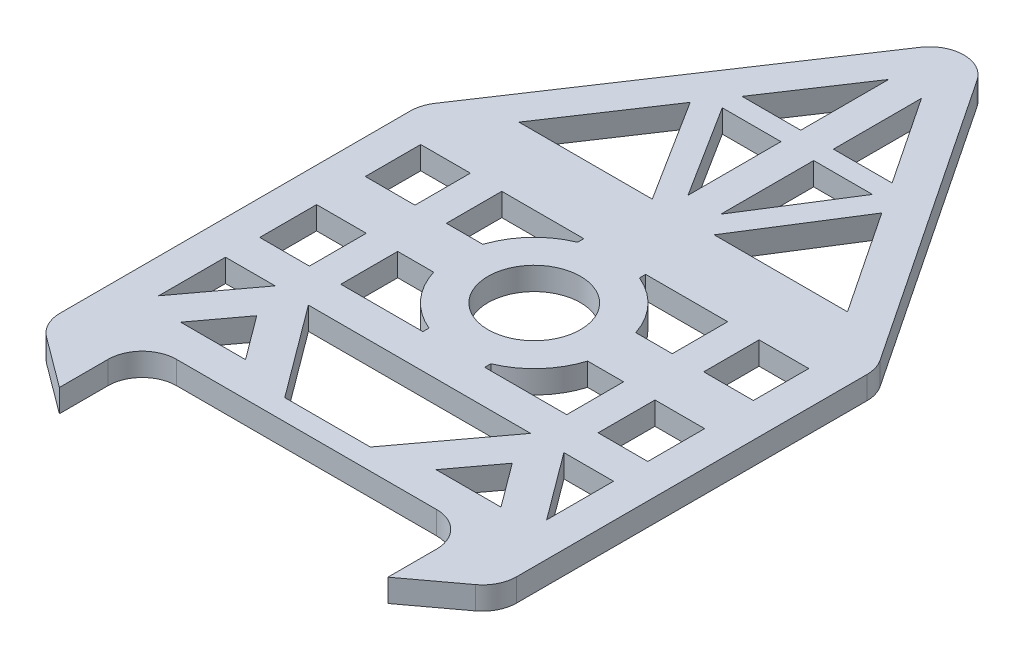
SolidWorks part; units mm, degrees
material "Cast Stainless Steel"
ref_plane "Front Plane" through (0, 0, 0) normal (0, 0, 1) x (1, 0, 0)
ref_plane "Top Plane" through (0, 0, 0) normal (0, 1, 0) x (1, 0, 0)
ref_plane "Right Plane" through (0, 0, 0) normal (1, 0, 0) x (0, 0, -1)
sketch "Sketch1" plane through (0, 0, 0) normal (0, 1, 0) x (1, 0, 0)
  line L0 (-324.5, 0) -> (-36.6111, 0)
  line L1 (19.4444, 0) -> (19.4444, 300)
  line L2 (19.4444, 300) -> (-180.5556, 600)
  line L3 (-180.5556, 600) -> (-380.5556, 300)
  line L4 (-380.5556, 300) -> (-380.5556, 0)
  line L5 (-380.5556, 0) -> (-380.5556, -30.9894)
  line L6 (19.4444, 300) -> (25, 294.4444)
  line L7 (-350.5556, 98.9559) -> (-307.0461, 98.9559)
  line L8 (-350.5556, 40.385) -> (-307.0461, 98.9559)
  line L9 (-218.053, 18.3812) -> (-277.9079, 98.9559)
  line L10 (-143.0581, 18.3812) -> (-83.2032, 98.9559)
  line L11 (-40.2128, 30) -> (-97.0554, 30)
  line L12 (-350.5556, 128.9559) -> (-307.0461, 128.9559)
  line L13 (-194.896, 524.4061) -> (-246.3088, 447.2869)
  line L14 (-36.6111, 330) -> (-96.6333, 420.0334)
  line L15 (-324.5, 330) -> (-207.6471, 330)
  line L16 (-10.5556, 40.385) -> (-54.065, 98.9559)
  line L17 (-180.5556, 545.9167) -> (-355.594, 283.359) construction
  line L18 (-5.5171, 283.359) -> (-180.5556, 545.9167) construction
  line L19 (-350.5556, 270) -> (-307.0461, 270)
  line L20 (-350.5556, 270) -> (-350.5556, 221.4578)
  line L21 (-10.5556, 128.9559) -> (-10.5556, 178.791)
  line L22 (-350.5556, 300) -> (-350.5556, 0) construction
  line L23 (-380.5556, -30.9894) -> (-324.5, -72.6302)
  line L24 (-380.5556, 128.9559) -> (19.4444, 128.9559) construction
  line L25 (-292.477, 115.7535) -> (-292.477, 91.7007) construction
  line L26 (-97.0554, 30) -> (-68.6341, 68.2598)
  line L27 (-218.053, 18.3812) -> (-143.0581, 18.3812)
  line L28 (-40.2128, 30) -> (-68.6341, 68.2598)
  line L29 (-320.8984, 30) -> (-264.0557, 30)
  line L30 (-153.464, 330) -> (-36.6111, 330)
  line L31 (-320.8984, 30) -> (-292.477, 68.2598)
  line L32 (-54.065, 98.9559) -> (-10.5556, 98.9559)
  line L33 (-277.9079, 98.9559) -> (-83.2032, 98.9559)
  line L34 (-264.0557, 30) -> (-292.477, 68.2598)
  line L35 (-380.5556, 98.9559) -> (19.4444, 98.9559) construction
  line L36 (-324.5, -72.6302) -> (-324.5, 0)
  line L37 (-36.6111, -72.6302) -> (-36.6111, 0)
  line L38 (-246.3088, 447.2869) -> (-194.896, 447.2869)
  line L39 (-350.5556, 221.4578) -> (-307.0461, 221.4578)
  line L40 (-350.5556, 178.791) -> (-307.0461, 178.791)
  line L41 (-180.5556, 424.8555) -> (-180.5556, 353.486) construction
  line L42 (-10.5556, 178.791) -> (-54.065, 178.791)
  line L43 (-10.5556, 221.4578) -> (-54.065, 221.4578)
  line L44 (-307.0461, 270) -> (-307.0461, 221.4578)
  line L45 (-279.5115, 270) -> (-279.5115, 221.4578)
  line L46 (-548.4441, 199.478) -> (-478.3267, 199.478) construction
  line L47 (-307.0461, 128.9559) -> (-307.0461, 178.791)
  line L48 (-279.5115, 128.9559) -> (-279.5115, 178.791)
  line L49 (19.4444, -30.9894) -> (-36.6111, -72.6302)
  line L50 (19.4444, 0) -> (19.4444, -30.9894)
  line L51 (-380.5556, 0) -> (-380.5556, -30.9894)
  line L52 (19.4444, 0) -> (19.4444, -30.9894)
  line L53 (-350.5556, 98.9559) -> (-350.5556, 40.385)
  line L54 (-10.5556, 98.9559) -> (-10.5556, 40.385)
  line L55 (-207.6471, 134.3673) -> (-207.6471, 128.9559)
  line L56 (-153.464, 134.3673) -> (-153.464, 128.9559)
  line L57 (-207.6471, 264.5887) -> (-207.6471, 270)
  line L58 (-153.464, 264.5887) -> (-153.464, 270)
  line L59 (-81.5996, 128.9559) -> (-81.5996, 178.791)
  line L60 (-54.065, 128.9559) -> (-54.065, 178.791)
  line L61 (-81.5996, 270) -> (-81.5996, 221.4578)
  line L62 (-54.065, 270) -> (-54.065, 221.4578)
  line L63 (-350.5556, 178.791) -> (-350.5556, 128.9559)
  line L64 (-114.8023, 429.9922) -> (-166.2152, 429.9922)
  line L65 (-114.8023, 447.2869) -> (-166.2152, 524.4061)
  line L66 (-194.896, 524.4061) -> (-194.896, 447.2869)
  line L67 (-166.2152, 524.4061) -> (-166.2152, 447.2869)
  line L68 (-246.3088, 429.9922) -> (-194.896, 348.542)
  line L69 (-264.4778, 420.0334) -> (-207.6471, 330)
  line L70 (-114.8023, 429.9922) -> (-166.2152, 348.542)
  line L71 (-96.6333, 420.0334) -> (-153.464, 330)
  line L72 (-166.2152, 447.2869) -> (-114.8023, 447.2869)
  line L73 (-194.896, 429.9922) -> (-246.3088, 429.9922)
  line L74 (-194.896, 429.9922) -> (-194.896, 348.542)
  line L75 (-166.2152, 429.9922) -> (-166.2152, 348.542)
  line L76 (-264.4778, 420.0334) -> (-324.5, 330)
  line L77 (-10.5556, 221.4578) -> (-10.5556, 270)
  line L78 (-81.5996, 178.791) -> (-113.1359, 178.791)
  line L79 (-81.5996, 221.4578) -> (-113.5463, 221.4578)
  line L80 (-279.5115, 178.791) -> (-247.9752, 178.791)
  line L81 (-279.5115, 221.4578) -> (-247.5648, 221.4578)
  line L82 (-279.5115, 270) -> (-207.6471, 270)
  line L83 (-279.5115, 128.9559) -> (-207.6471, 128.9559)
  line L84 (-54.065, 128.9559) -> (-10.5556, 128.9559)
  line L85 (-54.065, 270) -> (-10.5556, 270)
  line L86 (-153.464, 270) -> (-81.5996, 270)
  line L87 (-153.464, 128.9559) -> (-81.5996, 128.9559)
  arc A0 (-247.9752, 178.791) -> (-207.6471, 134.3673) centre (-180.5556, 199.478) ccw
  circle A1 centre (-180.5556, 199.478) radius 40.522
  arc A2 (-113.5463, 221.4578) -> (-153.464, 264.5887) centre (-180.5556, 199.478) ccw
  circle A3 centre (-180.5556, 199.478) radius 70.522 construction
  arc A4 (-207.6471, 264.5887) -> (-247.5648, 221.4578) centre (-180.5556, 199.478) ccw
  arc A5 (-153.464, 134.3673) -> (-113.1359, 178.791) centre (-180.5556, 199.478) ccw
  point P3 (-180.5556, 0)
  point P11 (-279.5115, 98.9559)
  point P13 (-81.5996, 98.9559)
  point P16 (-380.5556, 330)
  point P17 (19.4444, 330)
  point P23 (-10.5556, 0)
  point P24 (-10.5556, 300)
  point P25 (-380.5556, 270)
  point P26 (19.4444, 270)
  point P33 (-81.3793, 56.7498)
  point P34 (-1.5461, -21.4335)
  point P35 (-180.5556, -42.4264)
  point P36 (-279.7318, 56.7498)
  point P37 (-359.565, -21.4335)
  point P38 (-380.5556, 30)
  point P39 (19.4444, 30)
  point P69 (-307.0461, 153.8735)
  point P74 (-356.4732, -17.8896)
  point P83 (-54.065, 153.8735)
  point P93 (-113.115, 220.0966)
  point P112 (-282.9637, 81.0663)
  point P113 (-228.4809, -17.8896)
  point P114 (-301.9903, 81.0663)
  point P115 (-380.5556, 30)
  dimension "D3" = 400
  dimension "D8" = 53.393
  dimension "D4" = 30
  dimension "D5" = 30
  dimension "D7" = 30
  dimension "D9" = 30
extrude "Boss-Extrude6" add sketch "Sketch1" along normal blind 20 contours L50 L1 L2 L3 L4 L5 L23 L36 L0 L37 L49 A1 L84 L60 L42 L21 L76 L69 L15 L75 L64 L70 L72 L67 L65 L71 L14 L30 L63 L40 L47 L12 L53 L7 L8 L34 L29 L31 L28 L11 L26
fillet "Fillet1" radius 30 1 edges at (-180.5556, 10, -600)
fillet "Fillet2" radius 30 6 edges at (-324.5, 10, 0) (-36.6111, 10, 0) (19.4444, 10, 30.9894) (-380.5556, 10, 30.9894) (-380.5556, 10, -300) (19.4444, 10, -300)
